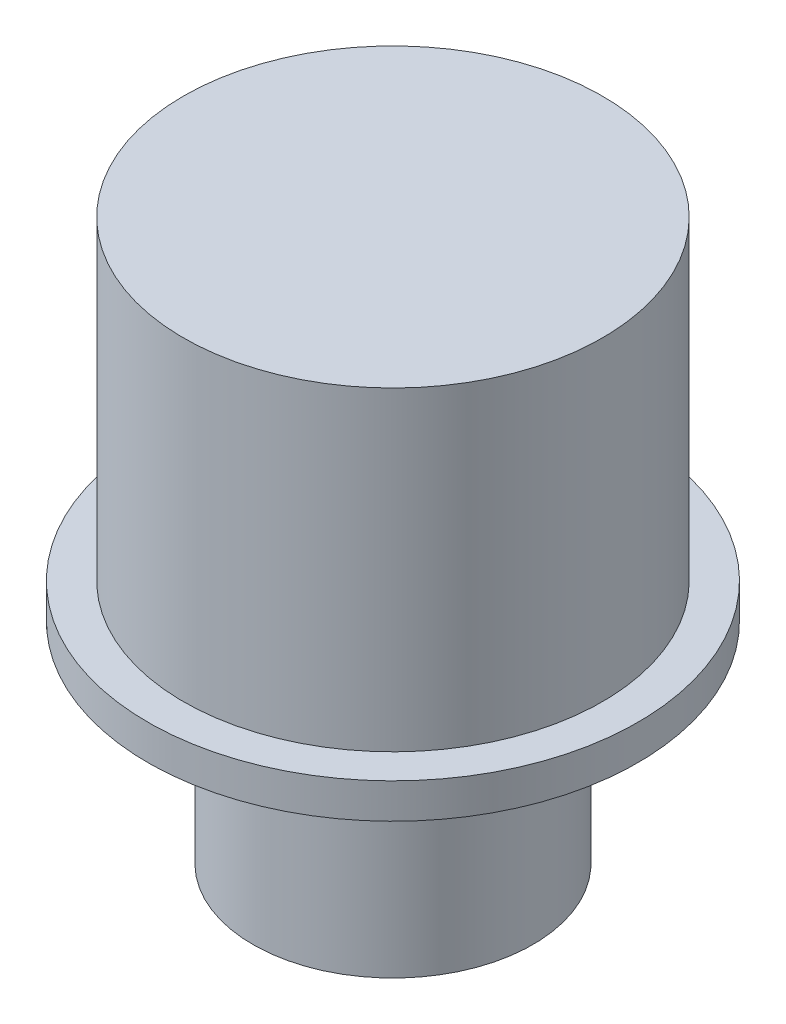
SolidWorks part; units mm, degrees
ref_plane "Front Plane" through (0, 0, 0) normal (0, 0, 1) x (1, 0, 0)
ref_plane "Top Plane" through (0, 0, 0) normal (0, 1, 0) x (1, 0, 0)
ref_plane "Right Plane" through (0, 0, 0) normal (1, 0, 0) x (0, 0, -1)
sketch "Sketch1" plane through (0, 0, 0) normal (0, 0, 1) x (1, 0, 0)
  line L0 (0, 0) -> (12.7, 0)
  line L1 (12.7, 0) -> (12.7, 19.05)
  line L2 (12.7, 19.05) -> (22.225, 19.05)
  line L3 (22.225, 19.05) -> (22.225, 22.225)
  line L4 (22.225, 22.225) -> (19, 22.225)
  line L5 (19, 22.225) -> (19, 50.8)
  line L6 (19, 50.8) -> (0, 50.8)
  line L7 (0, 50.8) -> (0, 0)
  dimension "D1" = 19
  dimension "D2" = 12.7
  dimension "D3" = 22.225
  dimension "D4" = 19.05
  dimension "D5" = 3.175
  dimension "D6" = 50.8
revolve "Revolve1" add sketch "Sketch1" angle 360 about L7
